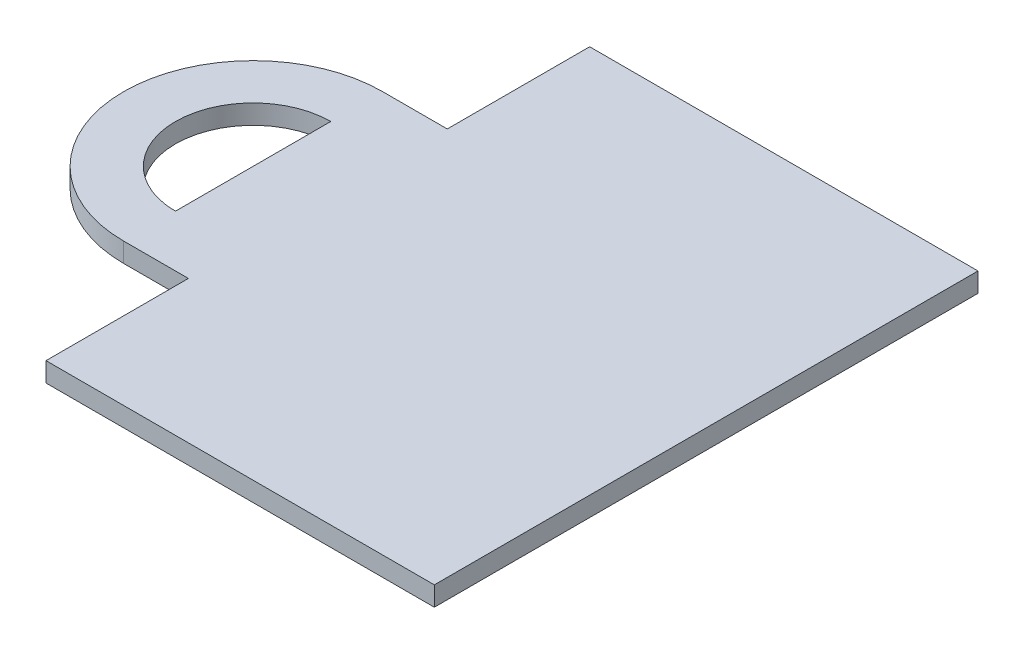
SolidWorks part; units mm, degrees
ref_plane "Front Plane" through (0, 0, 0) normal (0, 0, 1) x (1, 0, 0)
ref_plane "Top Plane" through (0, 0, 0) normal (0, 1, 0) x (1, 0, 0)
ref_plane "Right Plane" through (0, 0, 0) normal (1, 0, 0) x (0, 0, -1)
sketch "Sketch1" plane through (0, 0, 0) normal (0, 1, 0) x (1, 0, 0)
  line L0 (0, 0) -> (-150, 0)
  line L1 (0, 0) -> (0, -210)
  line L2 (0, -210) -> (-150, -210)
  line L3 (-150, 0) -> (-150, -55)
  line L4 (-150, -155) -> (-150, -210)
  line L5 (-150, -55) -> (-175, -55)
  line L6 (-150, -155) -> (-175, -155)
  line L7 (-175, -75) -> (-175, -135)
  arc A0 (-175, -55) -> (-175, -155) centre (-175, -105) ccw
  arc A1 (-175, -75) -> (-175, -135) centre (-175, -105) ccw
  point P13 (0, -105)
  dimension "D7" = 50
  dimension "D8" = 30
  dimension "D1" = 150
  dimension "D2" = 210
  dimension "D3" = 55
  dimension "D4" = 25
  dimension "D5" = 25
  dimension "D6" = 55
  dimension "D9" = 60
extrude "Boss-Extrude1" add sketch "Sketch1" along normal blind 7.5
